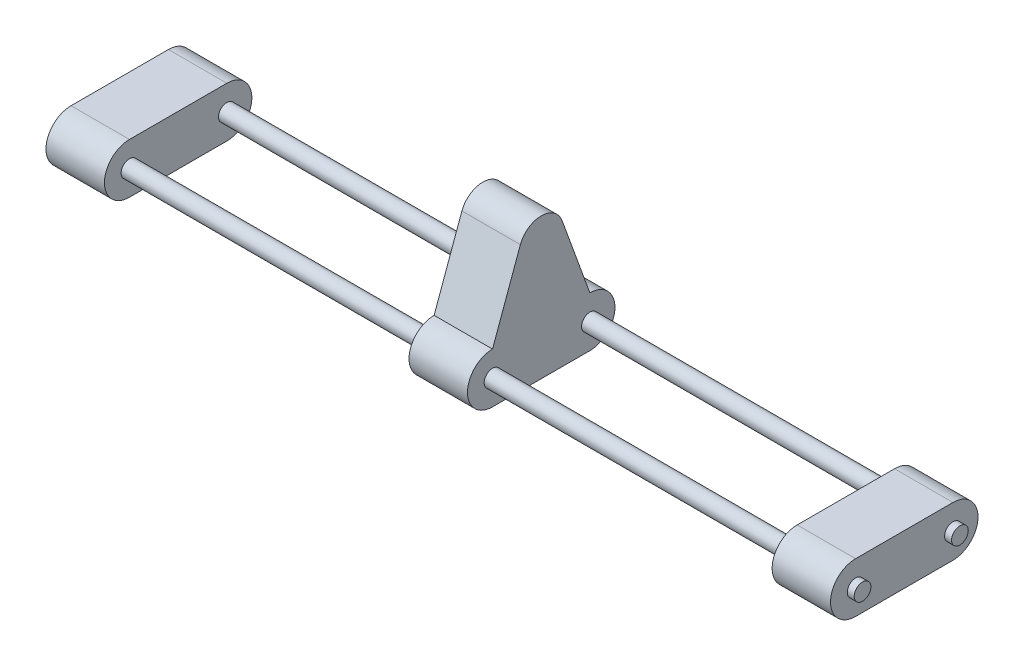
SolidWorks part; units mm, degrees
ref_plane "Ön Düzlem" through (0, 0, 0) normal (0, 0, 1) x (1, 0, 0)
ref_plane "Üst Düzlem" through (0, 0, 0) normal (0, 1, 0) x (1, 0, 0)
ref_plane "Sağ Düzlem" through (0, 0, 0) normal (1, 0, 0) x (0, 0, -1)
sketch "Çizim1" plane through (0, 0, 0) normal (1, 0, 0) x (0, 0, -1)
  line L0 (-35, 0) -> (35, 0) construction
  line L1 (-35, 18) -> (35, 18)
  line L2 (-35, -18) -> (35, -18)
  arc A0 (-35, 18) -> (-35, -18) centre (-35, 0) ccw
  arc A1 (35, -18) -> (35, 18) centre (35, 0) ccw
  circle A2 centre (-35, 0) radius 6
  circle A3 centre (35, 0) radius 6
  point P2 (0, 0)
  dimension "D3" = 12
  dimension "D4" = 12
  dimension "D1" = 70
  dimension "D2" = 36
extrude "Yükseklik-Ekstrüzyon1" add sketch "Çizim1" along normal mid plane 42
ref_plane "Düzlem1" through (-261, 0, 0) normal (-1, 0, 0) x (0, 0, 1)
sketch "Çizim2" plane through (-261, 0, 0) normal (-1, 0, 0) x (0, 0, 1)
  line L0 (0, 18) -> (0, 73) construction
  line L1 (15, 73) -> (-15, 73)
  line L2 (-35, -18) -> (35, -18)
  line L3 (35, 18) -> (-35, 18)
  line L4 (-35, -18) -> (35, -18)
  line L5 (35, 18) -> (-35, 18)
  line L6 (-15, 73) -> (-35, 18)
  line L7 (15, 73) -> (35, 18)
  circle A1 centre (35, 0) radius 6
  circle A2 centre (35, 0) radius 6
  circle A3 centre (-35, 0) radius 6
  circle A4 centre (-35, 0) radius 6
  arc A6 (35, -18) -> (35, 18) centre (35, 0) ccw
  arc A7 (-35, 18) -> (-35, -18) centre (-35, 0) ccw
  arc A8 (35, -18) -> (35, 18) centre (35, 0) ccw
  arc A9 (-35, 18) -> (-35, -18) centre (-35, 0) ccw
  point P18 (0, 73)
  dimension "D4" = 30
  dimension "D1" = 0
  dimension "D2" = 0
  dimension "D3" = 0
extrude "Yükseklik-Ekstrüzyon2" add sketch "Çizim2" along normal mid plane 42 separate body contours L0 L5 L7 L1 | L5 L0 L1 L6 | L5 A9 L4 A8 A2 A4
mirror "Aynalama1" about plane through (-261, 0, 0) normal (-1, 0, 0) of bodies 101
sketch "Çizim3" plane through (-261, 0, 0) normal (-1, 0, 0) x (0, 0, 1)
  circle A0 centre (-35, 0) radius 6 construction
  circle A1 centre (35, 0) radius 6 construction
  circle A5 centre (-35, 0) radius 6
  circle A6 centre (35, 0) radius 6
extrude "Yükseklik-Ekstrüzyon3" add sketch "Çizim3" against normal offset from surface 5 and the other way offset from surface (287 mm away) 5 up to face at (21, 0, 29) offset beyond the face yes other way up to face at (-543, 0, 29)
sketch "Çizim4" plane through (-240, 0, 0) normal (1, 0, 0) x (0, 0, -1)
  line L0 (-15, 73) -> (15, 73)
  line L6 (35, 18) -> (15, 73)
  line L7 (15, 73) -> (-15, 73)
  line L8 (-15, 73) -> (-35, 18)
  line L9 (-35, -18) -> (35, -18)
  line L10 (35, 18) -> (15, 73)
  line L12 (-15, 73) -> (-35, 18)
  line L13 (-35, -18) -> (35, -18)
  arc A1 (-15, 73) -> (15, 73) centre (0, 67.4543) cw
  arc A4 (-35, 18) -> (-35, -18) centre (-35, 0) ccw
  arc A5 (35, -18) -> (35, 18) centre (35, 0) ccw
  arc A6 (-35, 18) -> (-35, -18) centre (-35, 0) ccw
  arc A7 (35, -18) -> (35, 18) centre (35, 0) ccw
  line M3 (15, 73) -> (-15, 73)
  dimension "D1" = 0
extrude "Yükseklik-Ekstrüzyon4" add sketch "Çizim4" against normal blind 42 contours A1 M3
